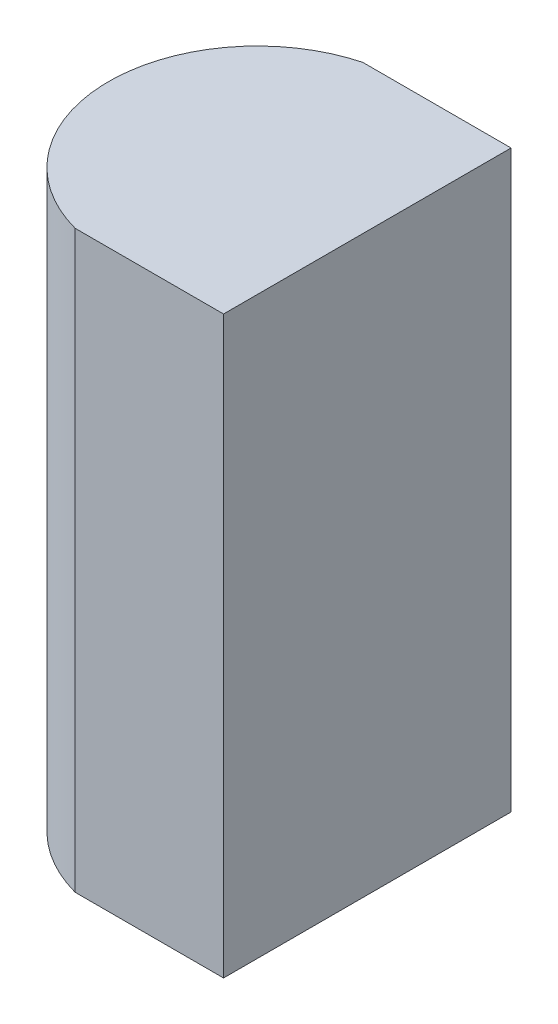
SolidWorks part; units mm, degrees
ref_plane "前视基准面" through (0, 0, 0) normal (0, 0, 1) x (1, 0, 0)
ref_plane "上视基准面" through (0, 0, 0) normal (0, 1, 0) x (1, 0, 0)
ref_plane "右视基准面" through (0, 0, 0) normal (1, 0, 0) x (0, 0, -1)
sketch "草图1" plane through (0, 0, 0) normal (0, 1, 0) x (1, 0, 0)
  line L0 (0, 0) -> (0, -4)
  line L1 (0, 0) -> (-2.0638, 0)
  line L2 (0, -4) -> (-2.0638, -4)
  line L3 (0, -2) -> (6.7931, -2) construction
  arc A0 (-2.0638, 0) -> (-2.0638, -4) centre (-1.53, -2) ccw
  point P7 (-3.6, -2)
  dimension "D2" = 2.07
  dimension "D3" = 3.6
  dimension "D1" = 4
extrude "凸台-拉伸1" add sketch "草图1" along normal blind 8
